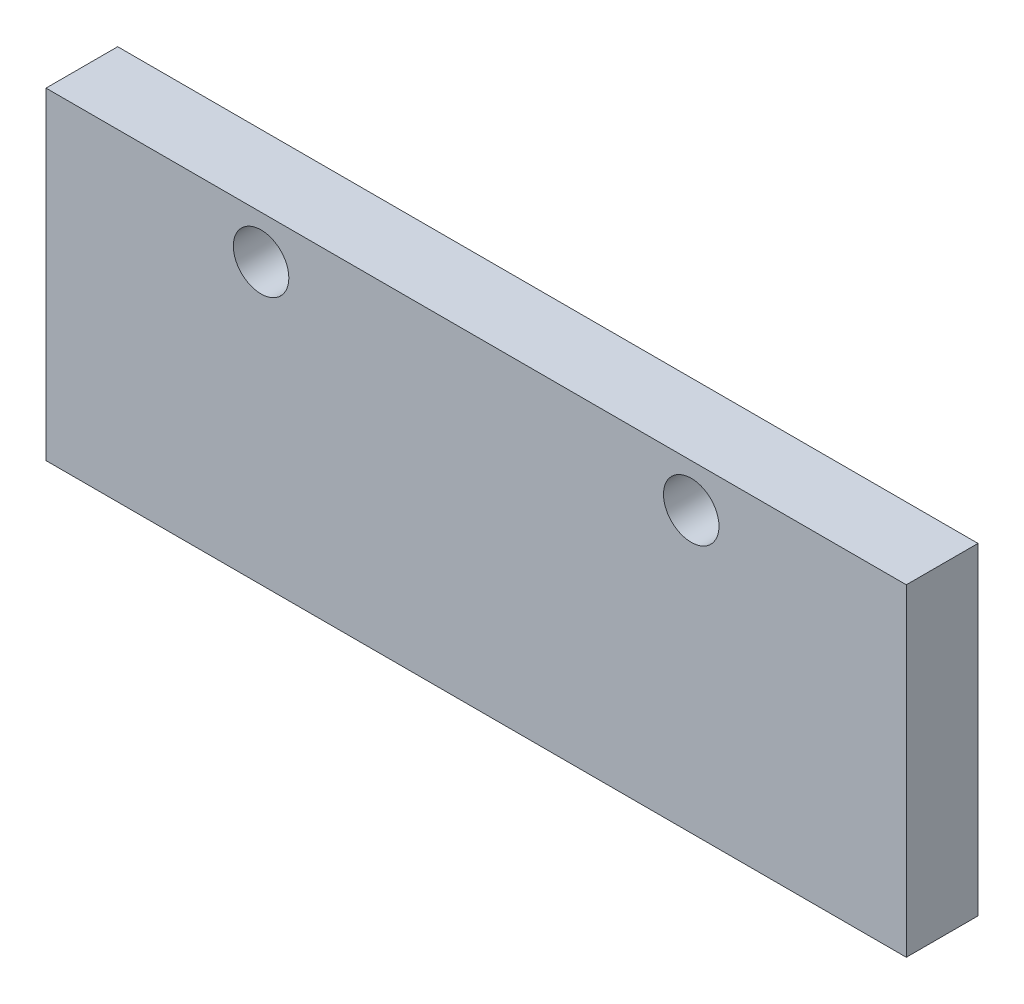
SolidWorks part; units mm, degrees
ref_plane "Front Plane" through (0, 0, 0) normal (0, 0, 1) x (1, 0, 0)
ref_plane "Top Plane" through (0, 0, 0) normal (0, 1, 0) x (1, 0, 0)
ref_plane "Right Plane" through (0, 0, 0) normal (1, 0, 0) x (0, 0, -1)
sketch "Sketch1" plane through (0, 0, 0) normal (0, 0, 1) x (1, 0, 0)
  line L1 (-38.1, 14.2875) -> (38.1, 14.2875)
  line L2 (-38.1, 14.2875) -> (-38.1, -14.2875)
  line L3 (-38.1, -14.2875) -> (38.1, -14.2875)
  line L4 (38.1, 14.2875) -> (38.1, -14.2875)
  line L5 (-38.1, 14.2875) -> (38.1, -14.2875) construction
  line L6 (-38.1, -14.2875) -> (38.1, 14.2875) construction
  point P0 (0, 0)
  dimension "D1" = 28.575
  dimension "D2" = 76.2
extrude "Boss-Extrude1" add sketch "Sketch1" along normal blind 6.35
hole_wizard "#10 (0.1935) Diameter Hole1" positions "Sketch3" profile "Sketch2" hole size "#10" standard "ANSI Inch" end condition up to next
sketch "Sketch3" plane through (0, 0, 6.35) normal (0, 0, 1) x (1, 0, 0)
  line L0 (-19.05, 10.4775) -> (19.05, 10.4775) construction
  line L1 (0, 10.4775) -> (0, 0) construction
  line L2 (38.1, 14.2875) -> (-38.1, 14.2875) construction
  point P0 (-19.05, 10.4775)
  point P2 (19.05, 10.4775)
  dimension "D1" = 38.1
  dimension "D2" = 3.81
sketch "Sketch2" plane through (-19.05, 10.4775, 6.35) normal (1, 0, 0) x (0, -1, 0)
  line L0 (0, 0) -> (0, 6.35)
  line L1 (0, 6.35) -> (2.4574, 6.35)
  line L2 (2.4574, 6.35) -> (2.4574, 0)
  line L5 (2.4574, 0) -> (0, 0)
  line L11 (0, -6.35) -> (0, 107.95) construction
  dimension "Thru Hole Dia." = 4.9149
  dimension "Thru Hole Depth" = 6.35
